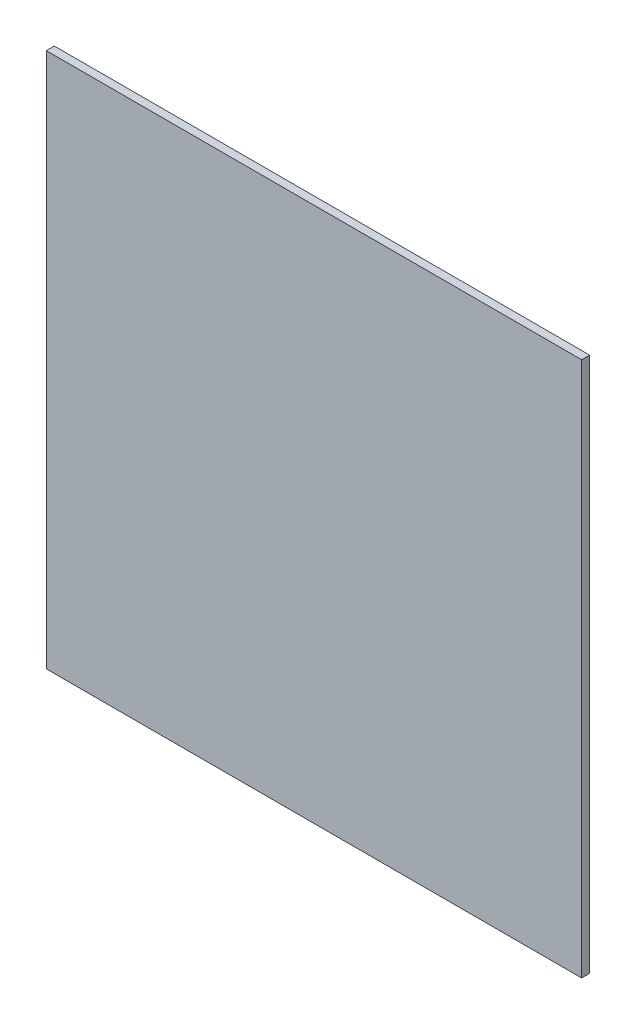
SolidWorks part; units mm, degrees
material "Verre"
ref_plane "Plan de face" through (0, 0, 0) normal (0, 0, 1) x (1, 0, 0)
ref_plane "Plan de dessus" through (0, 0, 0) normal (0, 1, 0) x (1, 0, 0)
ref_plane "Plan de droite" through (0, 0, 0) normal (1, 0, 0) x (0, 0, -1)
sketch "Esquisse1" plane through (0, 0, 0) normal (0, 0, 1) x (1, 0, 0)
  line L1 (-106.9868, -295.6053) -> (93.0132, -295.6053)
  line L2 (-106.9868, -295.6053) -> (-106.9868, -495.6053)
  line L3 (-106.9868, -495.6053) -> (93.0132, -495.6053)
  line L4 (93.0132, -295.6053) -> (93.0132, -495.6053)
  dimension "D1" = 200
extrude "Boss.-Extru.1" add sketch "Esquisse1" along normal blind 3
